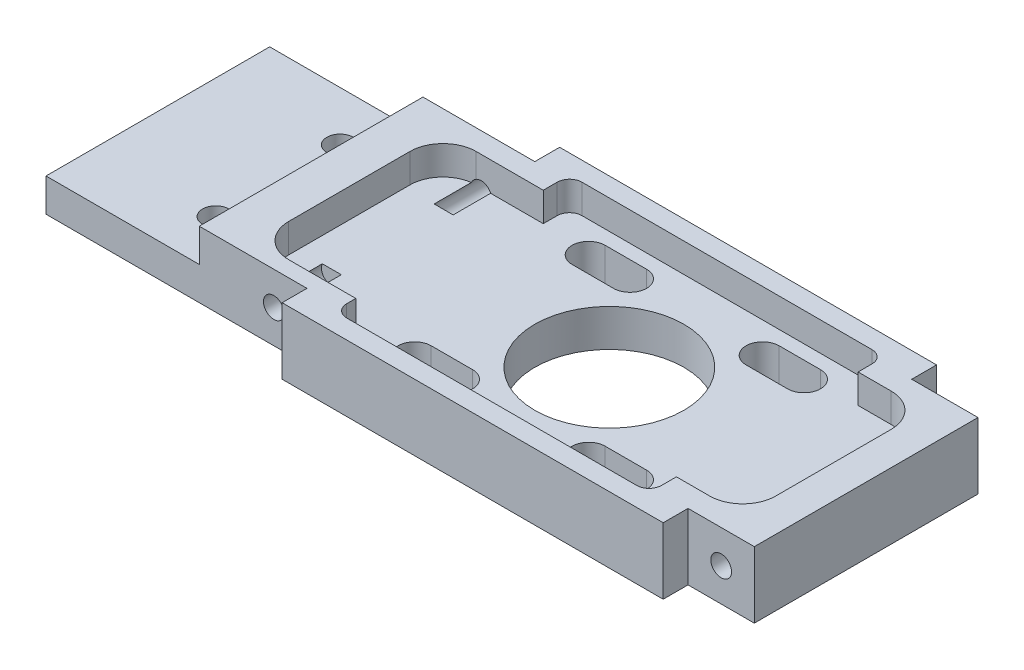
SolidWorks part; units mm, degrees
ref_plane "Спереди" through (0, 0, 0) normal (0, 0, 1) x (1, 0, 0)
ref_plane "Сверху" through (0, 0, 0) normal (0, 1, 0) x (1, 0, 0)
ref_plane "Справа" through (0, 0, 0) normal (1, 0, 0) x (0, 0, -1)
sketch "Эскиз1" plane through (0, 0, 0) normal (0, 1, 0) x (1, 0, 0)
  line L0 (43, 13.5) -> (43, -13.5)
  line L1 (-42.5, 13.5) -> (-10.5, 13.5)
  line L3 (-11, -13.5) -> (-42.5, -13.5)
  line L4 (43, -13.5) -> (35, -13.5)
  line L5 (35, -13.5) -> (35, -16.5)
  line L6 (35, -16.5) -> (-11, -16.5)
  line L7 (-42.5, -13.5) -> (-42.5, 13.5)
  line L8 (-11, -13.5) -> (-11, -16.5)
  line L10 (43, 13.5) -> (35, 13.5)
  line L11 (35, 13.5) -> (35, 16.5)
  line L12 (35, 16.5) -> (-10.5, 16.5)
  line L13 (-10.5, 13.5) -> (-10.5, 16.5)
  dimension "D1" = 85.5
  dimension "D3" = 27
  dimension "D4" = 43
  dimension "D5" = 8
  dimension "D6" = 46
  dimension "D7" = 3
extrude "Бобышка-Вытянуть1" add sketch "Эскиз1" along normal blind 8
sketch "Эскиз2" plane through (0, 8, 0) normal (0, 1, 0) x (1, 0, 0)
  line L0 (-10.5, 13.5) -> (-42.5, 13.5) construction
  line L1 (-42.5, -13.5) -> (-24, -13.5)
  line L2 (-42.5, -13.5) -> (-42.5, 13.5)
  line L3 (-42.5, 13.5) -> (-24, 13.5)
  line L4 (-24, -13.5) -> (-24, 13.5)
  dimension "D1" = 18.5
extrude "Вырез-Вытянуть1" cut sketch "Эскиз2" against normal blind 4
sketch "Эскиз3" plane through (0, 4, 0) normal (0, 1, 0) x (1, 0, 0)
  line L0 (-66.9295, 0) -> (61.2083, 0) construction
  circle A0 centre (-28, 7.5) radius 1.6
  circle A1 centre (-28, -7.5) radius 1.6
  dimension "D1" = 3.2
  dimension "D2" = 4
  dimension "D3" = 6
extrude "Вырез-Вытянуть2" cut sketch "Эскиз3" against normal through all
sketch "Эскиз4" plane through (0, 0, 0) normal (0, -1, 0) x (1, 0, 0)
  line L2 (-48.799, 10.5) -> (83.8179, 10.5) construction
  line L3 (75.0347, -10.5) -> (-48.1033, -10.5) construction
  line L4 (1.5, 30.4473) -> (1.5, -29.6953) construction
  line L5 (22.5, 25.5822) -> (22.5, -27.4305) construction
  line L6 (20, 10.5) -> (25, 10.5) construction
  line L7 (20, 12.5) -> (25, 12.5)
  line L8 (20, 8.5) -> (25, 8.5)
  line L9 (12, 38.8262) -> (12, -40.274) construction
  line L10 (4, 10.5) -> (-1, 10.5) construction
  line L11 (4, 12.5) -> (-1, 12.5)
  line L12 (4, 8.5) -> (-1, 8.5)
  line L13 (-58.5303, 0) -> (97.9894, 0) construction
  line L14 (20, -10.5) -> (25, -10.5) construction
  line L15 (20, -12.5) -> (25, -12.5)
  line L16 (20, -8.5) -> (25, -8.5)
  line L17 (4, -10.5) -> (-1, -10.5) construction
  line L18 (4, -12.5) -> (-1, -12.5)
  line L19 (4, -8.5) -> (-1, -8.5)
  circle A0 centre (12, 0) radius 9
  arc A1 (20, 12.5) -> (20, 8.5) centre (20, 10.5) ccw
  arc A2 (25, 8.5) -> (25, 12.5) centre (25, 10.5) ccw
  arc A3 (4, 12.5) -> (4, 8.5) centre (4, 10.5) cw
  arc A4 (-1, 8.5) -> (-1, 12.5) centre (-1, 10.5) cw
  arc A5 (20, -12.5) -> (20, -8.5) centre (20, -10.5) cw
  arc A6 (25, -8.5) -> (25, -12.5) centre (25, -10.5) cw
  arc A7 (4, -12.5) -> (4, -8.5) centre (4, -10.5) ccw
  arc A8 (-1, -8.5) -> (-1, -12.5) centre (-1, -10.5) ccw
  point P15 (22.5, 10.5)
  point P24 (1.5, 10.5)
  point P34 (22.5, -10.5)
  point P41 (1.5, -10.5)
  dimension "D1" = 18
  dimension "D2" = 23
  dimension "D3" = 10.5
  dimension "D4" = 10.5
  dimension "D5" = 10.5
  dimension "D6" = 10.5
  dimension "D7" = 4
  dimension "D8" = 5
extrude "Вырез-Вытянуть3" cut sketch "Эскиз4" against normal through all
sketch "Эскиз5" plane through (0, 8, 0) normal (0, 1, 0) x (1, 0, 0)
  line L4 (-7, 14.2) -> (-7, 11.0234) construction
  line L5 (-7, 11.0234) -> (-19.0995, 11.0234) construction
  line L6 (-7, -14.2) -> (-7, -11.6043) construction
  line L7 (-7, -11.6043) -> (-19.0995, -11.6043) construction
  line L8 (31, -14.2) -> (31, -10.9012) construction
  line L9 (31, -10.9012) -> (39, -10.9012) construction
  line L10 (31, 14.2) -> (31, 11.0234) construction
  line L11 (31, 11.0234) -> (39, 11.0234) construction
  line L12 (-19.0995, 7.0234) -> (-19.0995, -7.6043)
  line L13 (-15.0995, -11.6043) -> (-7, -11.6043)
  line L14 (-7, -11.6043) -> (-7, -12.7)
  line L15 (-5.5, -14.2) -> (29.5, -14.2)
  line L16 (31, -12.7) -> (31, -10.9012)
  line L17 (31, -10.9012) -> (35, -10.9012)
  line L18 (39, -6.9012) -> (39, 7.0234)
  line L19 (35, 11.0234) -> (31, 11.0234)
  line L20 (31, 11.0234) -> (31, 12.7)
  line L21 (29.5, 14.2) -> (-5.5, 14.2)
  line L22 (-7, 12.7) -> (-7, 11.0234)
  line L23 (-7, 11.0234) -> (-15.0995, 11.0234)
  arc A2 (39, 7.0234) -> (35, 11.0234) centre (35, 7.0234) ccw
  arc A3 (39, -6.9012) -> (35, -10.9012) centre (35, -6.9012) cw
  arc A4 (-19.0995, -7.6043) -> (-15.0995, -11.6043) centre (-15.0995, -7.6043) ccw
  arc A5 (-15.0995, 11.0234) -> (-19.0995, 7.0234) centre (-15.0995, 7.0234) ccw
  arc A6 (-7, -12.7) -> (-5.5, -14.2) centre (-5.5, -12.7) ccw
  arc A7 (31, -12.7) -> (29.5, -14.2) centre (29.5, -12.7) cw
  arc A8 (31, 12.7) -> (29.5, 14.2) centre (29.5, 12.7) ccw
  arc A9 (-5.5, 14.2) -> (-7, 12.7) centre (-5.5, 12.7) ccw
  dimension "D9" = 4
  dimension "D10" = 1.5
  dimension "D1" = 4
  dimension "D2" = 4
  dimension "D3" = 2.3
  dimension "D4" = 4
  dimension "D5" = 21.9246
  dimension "D6" = 2.3
  dimension "D7" = 12.0995
  dimension "D8" = 22.6277
extrude "Вырез-Вытянуть4" cut sketch "Эскиз5" against normal blind 3.5
sketch "Эскиз6" plane through (0, 0, 13.5) normal (0, 0, 1) x (1, 0, 0)
  circle A0 centre (39, 4) radius 1.25
  dimension "D1" = 2.5
  dimension "D2" = 4
  dimension "D3" = 4
extrude "Вырез-Вытянуть8" cut sketch "Эскиз6" against normal blind 7
sketch "Эскиз7" plane through (0, 0, 13.5) normal (0, 0, 1) x (1, 0, 0)
  circle A0 centre (-15, 4) radius 1.25
  dimension "D1" = 2.5
  dimension "D2" = 4
  dimension "D3" = 4
extrude "Вырез-Вытянуть9" cut sketch "Эскиз7" against normal blind 7
sketch "Эскиз8" plane through (0, 0, -13.5) normal (0, 0, -1) x (-1, 0, 0)
  circle A0 centre (-39, 4) radius 1.25
  dimension "D1" = 2.5
  dimension "D2" = 4
  dimension "D3" = 4
extrude "Вырез-Вытянуть10" cut sketch "Эскиз8" against normal blind 7
sketch "Эскиз9" plane through (0, 0, -13.5) normal (0, 0, -1) x (-1, 0, 0)
  circle A0 centre (14.5, 4) radius 1.25
  dimension "D1" = 2.5
  dimension "D2" = 4
  dimension "D3" = 4
extrude "Вырез-Вытянуть11" cut sketch "Эскиз9" against normal blind 7
